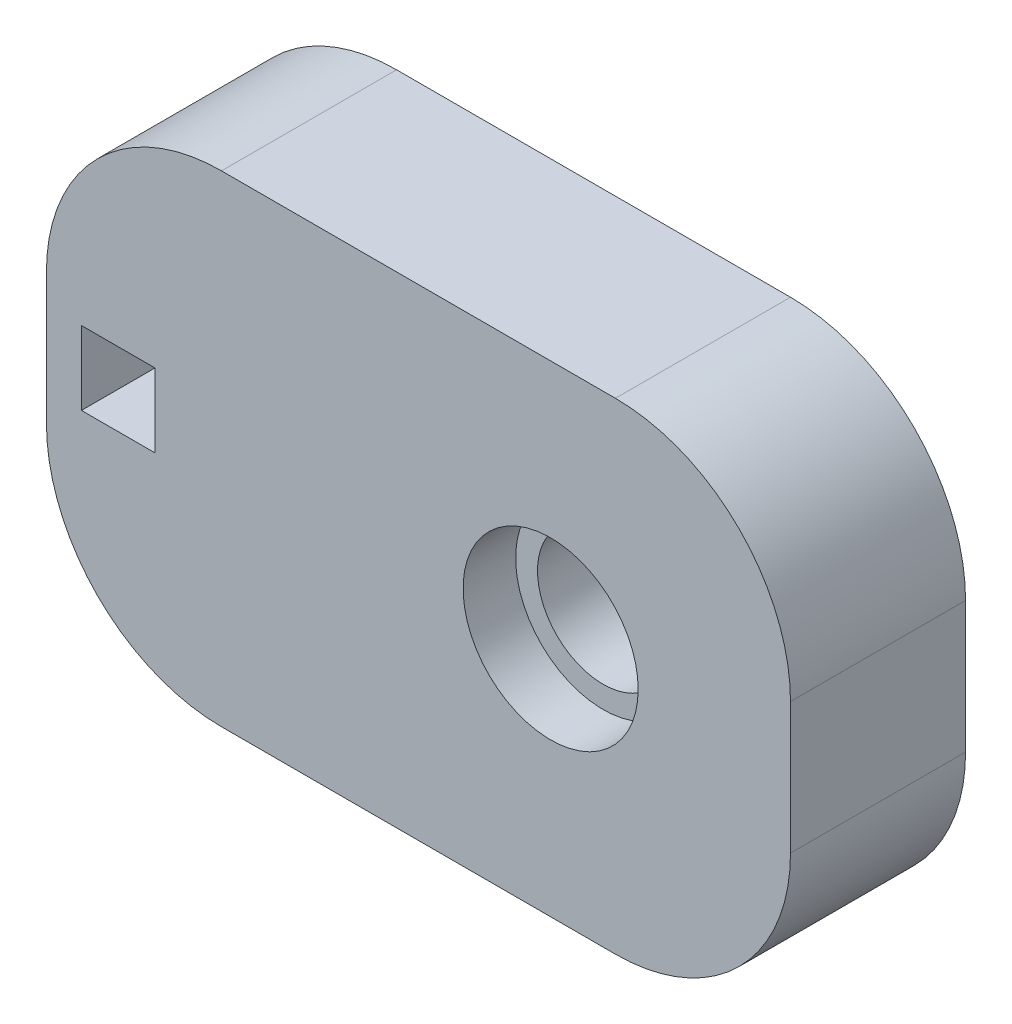
SolidWorks part; units mm, degrees
ref_plane "Front Plane" through (0, 0, 0) normal (0, 0, 1) x (1, 0, 0)
ref_plane "Top Plane" through (0, 0, 0) normal (0, 1, 0) x (1, 0, 0)
ref_plane "Right Plane" through (0, 0, 0) normal (1, 0, 0) x (0, 0, -1)
sketch "Sketch1" plane through (0, 0, 0) normal (0, 0, 1) x (1, 0, 0)
  line L1 (303.9256, -212.0087) -> (346.4256, -212.0087)
  line L3 (303.9256, -239.5087) -> (346.4256, -239.5087)
  line L4 (346.4256, -212.0087) -> (346.4256, -239.5087)
  line L5 (303.9256, -225.7587) -> (346.4256, -225.7587) construction
  line L8 (303.9256, -212.0087) -> (303.9256, -239.5087)
  point P0 (0, -31.3739)
  point P5 (0, 0)
  point P6 (0, 0)
  point P11 (0, 0)
  dimension "D1" = 42.5
  dimension "D2" = 27.5
extrude "Boss-Extrude1" add sketch "Sketch1" along normal blind 10 contours L8 L3 L4 L1
sketch "Sketch2" plane through (0, 0, 10) normal (0, 0, 1) x (1, 0, 0)
  line L6 (346.4256, -225.7587) -> (319.0256, -225.7587) construction
  line L7 (346.4256, -212.0087) -> (346.4256, -239.5087) construction
  circle A0 centre (332.7256, -225.7587) radius 5
  dimension "D1" = 10
  dimension "D2" = 13.7
extrude "Cut-Extrude1" cut sketch "Sketch2" against normal blind 3
sketch "Sketch3" plane through (0, 0, 10) normal (0, 0, 1) x (1, 0, 0)
  line L15 (346.4256, -225.7587) -> (149.3689, -225.7587) construction
  line L16 (346.4256, -212.0087) -> (346.4256, -239.5087) construction
  line L17 (303.9256, -212.0087) -> (303.9256, -239.5087) construction
  line L19 (310.1256, -223.6587) -> (305.9256, -223.6587)
  line L20 (310.1256, -227.8587) -> (310.1256, -223.6587)
  line L21 (305.9256, -227.8587) -> (310.1256, -227.8587)
  line L22 (305.9256, -223.6587) -> (305.9256, -227.8587)
  point P7 (305.9256, -225.7587)
  dimension "D1" = 4.2
  dimension "D2" = 2
extrude "Cut-Extrude2" cut sketch "Sketch3" against normal blind 5
sketch "Sketch4" plane through (0, 0, 10) normal (0, 0, 1) x (1, 0, 0)
  circle A0 centre (332.7256, -225.7587) radius 3.75
  dimension "D1" = 7.5
extrude "Cut-Extrude3" cut sketch "Sketch4" against normal offset from surface (7.5 mm away) 2.5 up to face at (325.1756, -225.7587, 0)
fillet "Fillet1" radius 10 4 edges at (346.4256, -239.5087, 5) (346.4256, -212.0087, 5) (303.9256, -239.5087, 5) (303.9256, -212.0087, 5)
